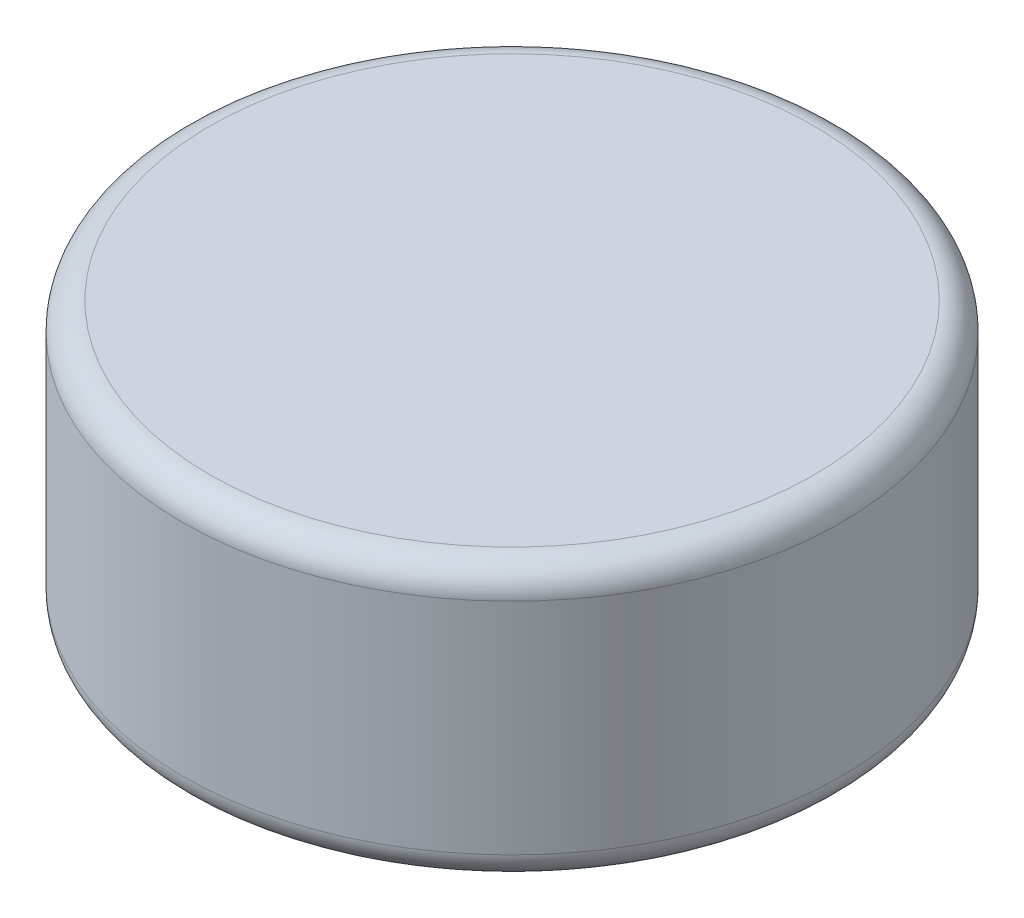
SolidWorks part; units mm, degrees
ref_plane "Front Plane" through (0, 0, 0) normal (0, 0, 1) x (1, 0, 0)
ref_plane "Top Plane" through (0, 0, 0) normal (0, 1, 0) x (1, 0, 0)
ref_plane "Right Plane" through (0, 0, 0) normal (1, 0, 0) x (0, 0, -1)
sketch "Sketch1" plane through (0, 0, 0) normal (0, 1, 0) x (1, 0, 0)
  circle A0 centre (0, 0) radius 3
  dimension "D1" = 6
extrude "Boss-Extrude1" add sketch "Sketch1" along normal blind 2.5
fillet "Fillet1" radius 0.25 2 edges at (0, 2.5, 3) (0, 0, 3)
